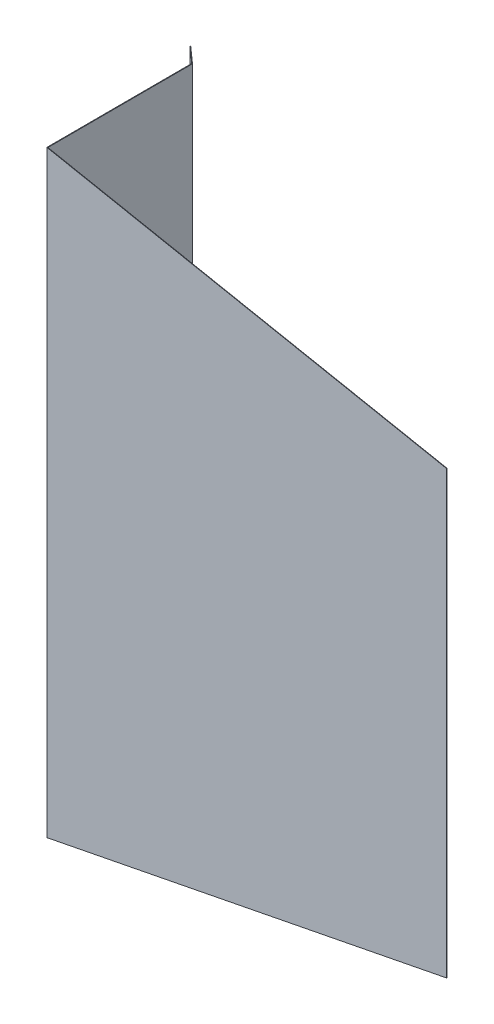
SolidWorks part; units mm, degrees
material "Zoltek Panex 33"
ref_plane "Płaszczyzna XY" through (0, 0, 0) normal (0, 0, 1) x (1, 0, 0)
ref_plane "Płaszczyzna XZ" through (0, 0, 0) normal (0, 1, 0) x (1, 0, 0)
ref_plane "Płaszczyzna YZ" through (0, 0, 0) normal (1, 0, 0) x (0, 0, -1)
ref_plane "Płaszczyzna2" through (260.8517, 0, -234.8719) normal (-0.7431, 0, 0.6691) x (0.6691, 0, 0.7431)
sketch "Szkic1" plane through (0, 0, 0) normal (0, 1, 0) x (1, 0, 0)
  line L0 (956.9819, -465.204) -> (970.6539, -477.0793)
  line L1 (970.6539, -477.0793) -> (970.6539, -617.9993)
  line L2 (970.6539, -617.9993) -> (1360.0727, -617.9993)
  dimension "D1" = 617.9993
  dimension "D2" = 140.92
  dimension "D3" = 130.977
  dimension "D4" = 18.1093
  dimension "D5" = 389.4188
  dimension "D6" = 970.6539
ref_plane "Płaszczyzna1" through (0, 0, 614.2832) normal (0, 0, 1) x (1, 0, 0)
sketch "Szkic2" plane through (0, 0, 614.2832) normal (0, 0, 1) x (1, 0, 0)
  line L0 (1353.3338, 216.7837) -> (973.6998, 291.1487) construction
  line L1 (218.0187, 0) -> (-218.0187, 0) construction
  line L2 (1353.3338, -216.7837) -> (973.6998, -291.1487) construction
  dimension "D1" = 216.7837
  dimension "D2" = 386.8489
  dimension "D3" = 291.1487
  dimension "D4" = 1353.3338
sketch "Szkic3" plane through (0, 0, 0) normal (0, 1, 0) x (1, 0, 0)
  line L0 (956.656, -465.5831) -> (969.8914, -477.0793)
  line L1 (969.8914, -477.0793) -> (970.0785, -618.4993)
  line L2 (970.0785, -618.4993) -> (1360.0727, -618.4993)
  line L3 (956.9819, -465.204) -> (970.6539, -477.0793) construction
  line L4 (970.6539, -617.9993) -> (1360.0727, -617.9993) construction
  dimension "D1" = 0.5
  dimension "D2" = 0.5
  dimension "D3" = 0.326
  dimension "D4" = 0.5754
extrude "Wyciągnięcie-cienka ścianka1" add sketch "Szkic3" along normal blind 400 and the other way blind 400 thin
ref_plane "Płaszczyzna3" through (90.906, 464.0758, 0) normal (0.1922, 0.9813, 0) x (-0.9813, 0.1922, 0)
ref_plane "Płaszczyzna4" through (90.906, -464.0758, 0) normal (-0.1922, 0.9813, 0) x (-0.9813, -0.1922, 0)
ref_plane "Płaszczyzna5" through (93.3263, -476.431, 0) normal (-0.1922, 0.9813, 0) x (-0.9813, -0.1922, 0)
ref_plane "Płaszczyzna6" through (93.5012, 477.3241, 0) normal (0.1922, 0.9813, 0) x (-0.9813, 0.1922, 0)
other "Cięcie powierzchnią1"
other "Cięcie powierzchnią2"
